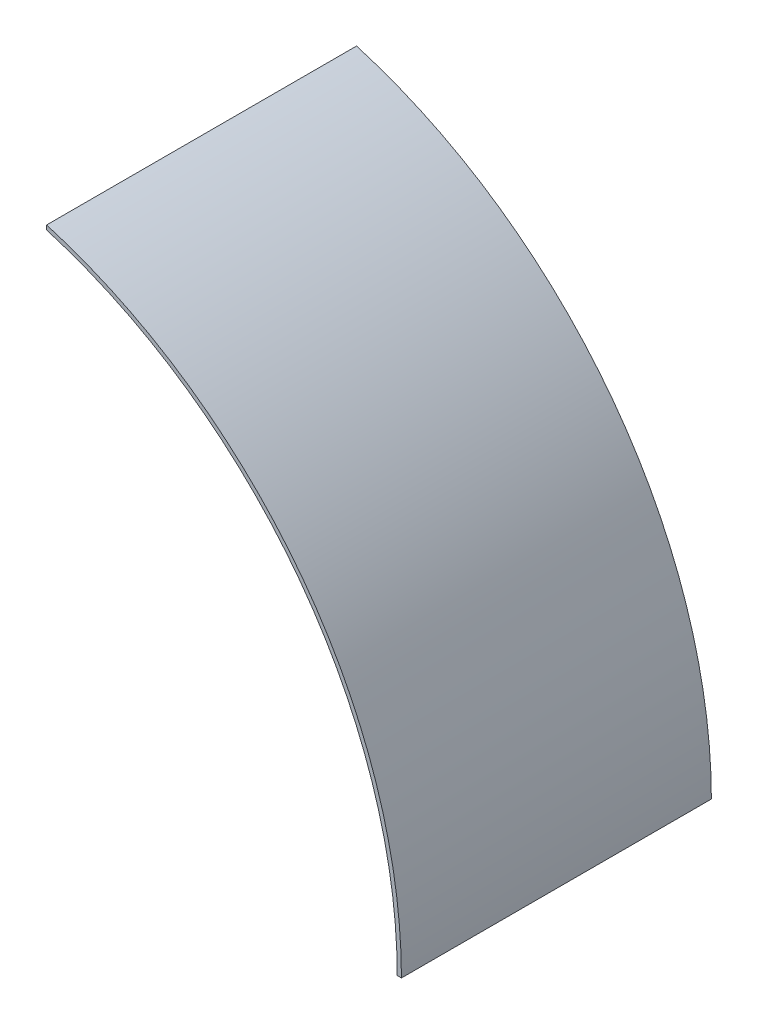
SolidWorks part; units mm, degrees
material "Plain Carbon Steel"
ref_plane "Front Plane" through (0, 0, 0) normal (0, 0, 1) x (1, 0, 0)
ref_plane "Top Plane" through (0, 0, 0) normal (0, 1, 0) x (1, 0, 0)
ref_plane "Right Plane" through (0, 0, 0) normal (1, 0, 0) x (0, 0, -1)
sketch "Sketch2" plane through (0, 0, 0) normal (0, 0, 1) x (1, 0, 0)
  line L0 (-177.8, 0) -> (177.8, 0) construction
  line L1 (0, 177.8) -> (0, -179.3189) construction
  line L2 (50.8, 0) -> (50.8, 108.9269) construction
  line L7 (50.8, 171.9728) -> (50.8, 170.3884)
  line L8 (0, -179.3189) -> (0, -160.382) construction
  line L21 (177.8, 0) -> (179.3189, 0)
  circle A0 centre (0, 0) radius 177.8 construction
  circle A1 centre (0, 0) radius 179.3189 construction
  arc A2 (50.8, 170.3884) -> (177.8, 0) centre (0, 0) cw
  arc A3 (179.3189, 0) -> (50.8, 171.9728) centre (0, 0) ccw
  dimension "D1" = 355.6
  dimension "D2" = 358.6378
  dimension "D3" = 50.8
extrude "Inner Ring - Right Side" add sketch "Sketch2" along normal blind 112.268
